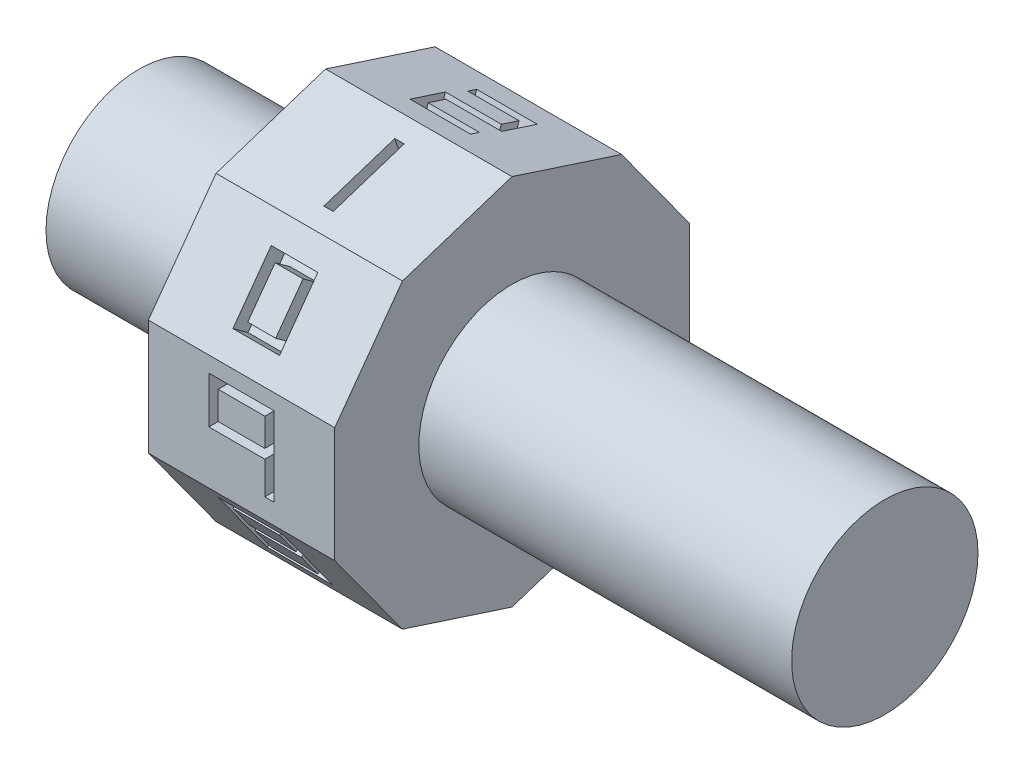
SolidWorks part; units mm, degrees
ref_plane "Front Plane" through (0, 0, 0) normal (0, 0, 1) x (1, 0, 0)
ref_plane "Top Plane" through (0, 0, 0) normal (0, 1, 0) x (1, 0, 0)
ref_plane "Right Plane" through (0, 0, 0) normal (1, 0, 0) x (0, 0, -1)
sketch "Sketch1" plane through (0, 0, 0) normal (1, 0, 0) x (0, 0, -1)
  line L1 (0, 25.4) -> (-14.9297, 20.549)
  line L2 (-14.9297, 20.549) -> (-24.1568, 7.849)
  line L3 (-24.1568, 7.849) -> (-24.1568, -7.849)
  line L4 (-24.1568, -7.849) -> (-14.9297, -20.549)
  line L5 (-14.9297, -20.549) -> (0, -25.4)
  line L6 (0, -25.4) -> (14.9297, -20.549)
  line L7 (14.9297, -20.549) -> (24.1568, -7.849)
  line L8 (24.1568, -7.849) -> (24.1568, 7.849)
  line L9 (24.1568, 7.849) -> (14.9297, 20.549)
  line L10 (14.9297, 20.549) -> (0, 25.4)
  circle A0 centre (0, 0) radius 24.1568 construction
  dimension "D1" = 25.4
extrude "Boss-Extrude1" add sketch "Sketch1" along normal blind 25.4
sketch "Sketch2" plane through (25.4, 0, 0) normal (1, 0, 0) x (0, 0, -1)
  circle A0 centre (0, 0) radius 12.7
  dimension "D1" = 25.4
extrude "Boss-Extrude2" add sketch "Sketch2" along normal blind 50.8
sketch "Sketch3" plane through (0, 0, 0) normal (-1, 0, 0) x (0, 0, 1)
  circle A0 centre (0, 0) radius 12.7
  dimension "D1" = 25.4
extrude "Boss-Extrude3" add sketch "Sketch3" along normal blind 25.4
sketch "Sketch4" plane through (0, 14.199, 19.5433) normal (0, 0.5878, 0.809) x (1, 0, 0)
  line L0 (0, 0) -> (25.4, 0) construction
  line L1 (25.4, -12.7) -> (25.4, 12.7) construction
  line L2 (12.7, 7.849) -> (12.7, -7.849) construction
  line L3 (25.4, 7.849) -> (0, 7.849) construction
  line L4 (25.4, -7.849) -> (0, -7.849) construction
  line L5 (10.16, 0) -> (15.24, 0)
  line L6 (15.24, -3.81) -> (15.24, 3.81)
  line L7 (10.16, -3.81) -> (10.16, 3.81)
  line L8 (10.16, 3.81) -> (15.24, 3.81)
  line L9 (10.16, -3.81) -> (15.24, -3.81)
  line L10 (10.795, 3.175) -> (14.605, 3.175)
  line L11 (14.605, -3.175) -> (14.605, 3.175)
  line L12 (10.795, -3.175) -> (14.605, -3.175)
  line L13 (10.795, -3.175) -> (10.795, 3.175)
  line L14 (9.525, 4.445) -> (15.875, 4.445)
  line L15 (15.875, -4.445) -> (15.875, 4.445)
  line L16 (9.525, -4.445) -> (15.875, -4.445)
  line L17 (9.525, -4.445) -> (9.525, 4.445)
  point P14 (12.7, 0)
  point P17 (15.24, 0)
  point P20 (10.16, 0)
  dimension "D1" = 5.08
  dimension "D2" = 7.62
  dimension "D3" = 0.635
  dimension "D4" = 0.635
extrude "Cut-Extrude1" cut sketch "Sketch4" against normal blind 2.54 contours L14 L15 L16 L17 | L10 L11 L12 L13
sketch "Sketch5" plane through (0, 22.9745, 7.4649) normal (0, 0.9511, 0.309) x (1, 0, 0)
  line L0 (12.7, -7.849) -> (12.7, 7.849) construction
  line L1 (25.4, -7.849) -> (0, -7.849) construction
  line L2 (25.4, 7.849) -> (0, 7.849) construction
  line L3 (12.7, -5.08) -> (12.7, 5.08)
  line L4 (13.335, -5.08) -> (13.335, 5.08)
  line L5 (12.065, -5.08) -> (12.065, 5.08)
  line L6 (12.065, 5.08) -> (13.335, 5.08)
  line L7 (13.335, -5.08) -> (12.065, -5.08)
  point P9 (12.7, 0)
  dimension "D1" = 10.16
  dimension "D2" = 0.635
  dimension "D3" = 0.635
extrude "Cut-Extrude2" cut sketch "Sketch5" against normal blind 2.54 contours L5 L6 L4 L7
sketch "Sketch6" plane through (0, 22.9745, -7.4649) normal (0, 0.9511, -0.309) x (1, 0, 0)
  line L0 (12.7, 7.849) -> (12.7, -7.849) construction
  line L1 (25.4, 7.849) -> (0, 7.849) construction
  line L2 (25.4, -7.849) -> (0, -7.849) construction
  line L3 (8.89, 3.81) -> (16.51, 3.81)
  line L4 (8.89, 0) -> (16.51, 0)
  line L5 (8.89, -3.81) -> (16.51, -3.81)
  line L6 (16.51, 3.81) -> (16.51, 0)
  line L7 (8.89, 0) -> (8.89, -3.81)
  line L8 (8.89, 3.175) -> (15.875, 3.175)
  line L9 (15.875, 3.175) -> (15.875, 0.635)
  line L10 (8.255, 0.635) -> (15.875, 0.635)
  line L11 (8.255, 0.635) -> (8.255, -4.445)
  line L12 (8.255, -4.445) -> (16.51, -4.445)
  line L13 (8.89, 4.445) -> (17.145, 4.445)
  line L14 (17.145, 4.445) -> (17.145, -0.635)
  line L15 (9.525, -0.635) -> (17.145, -0.635)
  line L16 (9.525, -0.635) -> (9.525, -3.175)
  line L17 (9.525, -3.175) -> (16.51, -3.175)
  line L18 (8.89, 4.445) -> (8.89, 3.175)
  line L19 (16.51, -3.175) -> (16.51, -4.445)
  point P9 (12.7, 3.81)
  point P13 (12.7, 0)
  point P16 (12.7, -3.81)
  dimension "D1" = 3.81
  dimension "D2" = 3.81
  dimension "D3" = 7.62
  dimension "D4" = 0.635
  dimension "D5" = 0.635
extrude "Cut-Extrude3" cut sketch "Sketch6" against normal blind 2.54 contours L8 L9 L10 L11 L12 L19 L17 L16 L15 L14 L13 L18
sketch "Sketch8" plane through (0, 14.199, -19.5433) normal (0, 0.5878, -0.809) x (-1, 0, 0)
  line L0 (-12.7, 7.849) -> (-12.7, -7.849) construction
  line L1 (-25.4, 7.849) -> (0, 7.849) construction
  line L2 (-25.4, -7.849) -> (0, -7.849) construction
  line L3 (-8.89, -5.08) -> (-16.51, -5.08)
  line L4 (-8.89, 0) -> (-16.51, 0)
  line L5 (-8.89, 5.08) -> (-16.51, 5.08)
  line L6 (-16.51, -5.08) -> (-16.51, 5.08)
  line L7 (-8.89, -4.445) -> (-15.875, -4.445)
  line L8 (-15.875, -4.445) -> (-15.875, 4.445)
  line L9 (-8.89, 4.445) -> (-15.875, 4.445)
  line L10 (-8.89, 0.635) -> (-16.51, 0.635)
  line L11 (-8.89, -5.715) -> (-17.145, -5.715)
  line L12 (-17.145, -5.715) -> (-17.145, 5.715)
  line L13 (-8.89, 5.715) -> (-17.145, 5.715)
  line L14 (-8.89, -0.635) -> (-16.51, -0.635)
  line L15 (-8.89, -5.715) -> (-8.89, -4.445)
  line L16 (-8.89, -0.635) -> (-8.89, 0.635)
  line L17 (-8.89, 4.445) -> (-8.89, 5.715)
  point P9 (-12.7, -5.08)
  point P13 (-12.7, 0)
  point P16 (-12.7, 5.08)
  dimension "D1" = 10.16
  dimension "D2" = 5.08
  dimension "D3" = 7.62
  dimension "D4" = 0.635
  dimension "D5" = 0.635
extrude "Cut-Extrude4" cut sketch "Sketch8" against normal blind 2.54 contours L7 L0 L3 L15 | L3 L0 L11 L15 | L0 L13 L12 L11 L3 L6 L5 | L0 L7 L8 L14 L6 L3 | L0 L4 L8 L14 | L14 L8 L4 L6 | L8 L10 L6 L4 | L0 L10 L8 L4 | L4 L0 L14 L16 | L10 L0 L4 L16 | L0 L5 L6 L10 L8 L9 | L5 L0 L9 L17 | L13 L0 L5 L17
sketch "Sketch9" plane through (0, 0, -24.1568) normal (0, 0, -1) x (-1, 0, 0)
  line L0 (-12.7, -7.849) -> (-12.7, 7.849) construction
  line L1 (-25.4, -7.849) -> (0, -7.849) construction
  line L2 (-25.4, 7.849) -> (0, 7.849) construction
  line L3 (-8.89, 0) -> (-16.51, 0)
  line L4 (-16.51, 5.08) -> (-16.51, -5.08)
  line L5 (-8.89, 0) -> (-8.89, -5.08)
  line L6 (-9.525, -0.635) -> (-16.51, -0.635)
  line L7 (-9.525, -0.635) -> (-9.525, -5.08)
  line L8 (-17.145, 5.08) -> (-17.145, -5.08)
  line L9 (-8.255, 0.635) -> (-16.51, 0.635)
  line L10 (-8.255, 0.635) -> (-8.255, -5.08)
  line L11 (-15.875, 5.08) -> (-15.875, -5.08)
  line L12 (-8.255, -5.08) -> (-9.525, -5.08)
  line L13 (-15.875, -5.08) -> (-17.145, -5.08)
  line L14 (-17.145, 5.08) -> (-15.875, 5.08)
  point P10 (-12.7, 0)
  point P12 (-16.51, 0)
  dimension "D1" = 10.16
  dimension "D2" = 7.62
  dimension "D3" = 5.08
  dimension "D4" = 0.635
  dimension "D5" = 0.635
extrude "Cut-Extrude5" cut sketch "Sketch9" against normal blind 2.54 contours L0 L6 L7 L12 L5 L3 | L0 L3 L5 L12 L10 L9 | L6 L0 L3 L11 | L3 L0 L9 L11 | L11 L3 L4 L6 | L11 L9 L4 L3 | L13 L11 L6 L4 | L14 L8 L13 L4 | L14 L4 L9 L11
sketch "Sketch10" plane through (0, -14.199, -19.5433) normal (0, -0.5878, -0.809) x (-1, 0, 0)
  line L0 (-12.7, -7.849) -> (-12.7, 7.849) construction
  line L1 (-25.4, -7.849) -> (0, -7.849) construction
  line L2 (-25.4, 7.849) -> (0, 7.849) construction
  line L3 (-8.89, 0) -> (-16.51, 0)
  line L4 (-8.89, -5.08) -> (-16.51, -5.08)
  line L5 (-8.89, 5.08) -> (-16.51, 5.08)
  line L6 (-8.89, -5.08) -> (-8.89, 0)
  line L7 (-16.51, 0) -> (-16.51, 5.08)
  line L8 (-8.89, 5.715) -> (-17.145, 5.715)
  line L9 (-17.145, -0.635) -> (-17.145, 5.715)
  line L10 (-9.525, -0.635) -> (-17.145, -0.635)
  line L11 (-9.525, -4.445) -> (-9.525, -0.635)
  line L12 (-9.525, -4.445) -> (-16.51, -4.445)
  line L13 (-8.89, 4.445) -> (-15.875, 4.445)
  line L14 (-15.875, 0.635) -> (-15.875, 4.445)
  line L15 (-8.255, 0.635) -> (-15.875, 0.635)
  line L16 (-8.255, -5.715) -> (-8.255, 0.635)
  line L17 (-8.255, -5.715) -> (-16.51, -5.715)
  line L18 (-16.51, -5.715) -> (-16.51, -4.445)
  line L19 (-8.89, 4.445) -> (-8.89, 5.715)
  point P10 (-12.7, 0)
  point P13 (-12.7, -5.08)
  point P16 (-12.7, 5.08)
  dimension "D1" = 10.16
  dimension "D2" = 5.08
  dimension "D3" = 7.62
  dimension "D4" = 0.635
  dimension "D5" = 0.635
extrude "Cut-Extrude6" cut sketch "Sketch10" against normal blind 2.54 contours L12 L18 L17 L16 L15 L14 L13 L19 L8 L9 L10 L11
sketch "Sketch11" plane through (0, -22.9745, -7.4649) normal (0, -0.9511, -0.309) x (1, 0, 0)
  line L0 (12.7, 7.849) -> (12.7, -7.849) construction
  line L1 (25.4, 7.849) -> (0, 7.849) construction
  line L2 (25.4, -7.849) -> (0, -7.849) construction
  line L3 (8.89, 5.08) -> (16.51, 5.08)
  line L4 (16.51, 0) -> (9.525, 0)
  line L5 (8.89, -5.08) -> (16.51, -5.08)
  line L6 (16.51, 0) -> (16.51, -5.08)
  line L7 (8.89, -5.08) -> (8.89, 5.08)
  line L8 (15.875, -0.635) -> (9.525, -0.635)
  line L9 (15.875, -0.635) -> (15.875, -4.445)
  line L10 (9.525, -4.445) -> (15.875, -4.445)
  line L11 (9.525, -4.445) -> (9.525, 4.445)
  line L12 (9.525, 4.445) -> (16.51, 4.445)
  line L13 (17.145, 0.635) -> (9.525, 0.635)
  line L14 (17.145, 0.635) -> (17.145, -5.715)
  line L15 (8.255, -5.715) -> (17.145, -5.715)
  line L16 (8.255, -5.715) -> (8.255, 5.715)
  line L17 (8.255, 5.715) -> (16.51, 5.715)
  line L18 (16.51, 5.715) -> (16.51, 4.445)
  point P9 (12.7, 5.08)
  point P13 (12.7, 0)
  point P16 (12.7, -5.08)
  dimension "D1" = 5.08
  dimension "D2" = 10.16
  dimension "D3" = 7.62
  dimension "D4" = 6.985
  dimension "D5" = 0.635
  dimension "D6" = 0.635
extrude "Cut-Extrude7" cut sketch "Sketch11" against normal blind 2.54 and the other way through all contours L0 L3 L7 L5 L10 L11 L12 | L0 L17 L16 L15 L5 L7 L3 | L17 L0 L3 L18 | L3 L0 L12 L18 | L0 L13 L11 L4 | L0 L4 L11 L8 | L13 L0 L4 L6 L5 L15 L14 | L4 L0 L8 L9 L10 L5 L6
sketch "Sketch12" plane through (0, -22.9745, 7.4649) normal (0, -0.9511, 0.309) x (1, 0, 0)
  line L0 (12.7, 7.849) -> (12.7, -7.849) construction
  line L1 (25.4, 7.849) -> (0, 7.849) construction
  line L2 (25.4, -7.849) -> (0, -7.849) construction
  line L3 (8.89, 5.08) -> (16.51, 5.08)
  line L4 (16.51, 5.08) -> (16.51, -5.08)
  line L5 (8.89, 4.445) -> (15.875, 4.445)
  line L6 (15.875, 4.445) -> (15.875, -5.08)
  line L7 (8.89, 5.715) -> (17.145, 5.715)
  line L8 (17.145, 5.715) -> (17.145, -5.08)
  line L9 (8.89, 5.715) -> (8.89, 4.445)
  line L10 (15.875, -5.08) -> (17.145, -5.08)
  point P6 (16.51, 0)
  point P9 (12.7, 5.08)
  point P11 (12.7, 0)
  dimension "D1" = 7.62
  dimension "D2" = 10.16
  dimension "D3" = 0.635
  dimension "D4" = 0.635
extrude "Cut-Extrude8" cut sketch "Sketch12" against normal blind 2.54 contours L7 L8 L10 L6 L5 L9
sketch "Sketch13" plane through (0, -14.199, 19.5433) normal (0, -0.5878, 0.809) x (1, 0, 0)
  line L0 (12.7, 7.849) -> (12.7, -7.849) construction
  line L1 (25.4, 7.849) -> (0, 7.849) construction
  line L2 (25.4, -7.849) -> (0, -7.849) construction
  line L3 (9.525, 0) -> (15.875, 0)
  line L4 (8.89, 5.08) -> (16.51, 5.08)
  line L5 (8.89, -5.08) -> (16.51, -5.08)
  line L6 (16.51, 5.08) -> (16.51, -5.08)
  line L7 (8.89, 5.08) -> (8.89, -5.08)
  line L8 (8.255, 5.715) -> (17.145, 5.715)
  line L9 (17.145, 5.715) -> (17.145, -5.715)
  line L10 (8.255, -5.715) -> (17.145, -5.715)
  line L11 (8.255, 5.715) -> (8.255, -5.715)
  line L12 (9.525, -0.635) -> (15.875, -0.635)
  line L13 (9.525, 4.445) -> (15.875, 4.445)
  line L14 (15.875, 4.445) -> (15.875, -4.445)
  line L15 (9.525, -4.445) -> (15.875, -4.445)
  line L16 (9.525, 4.445) -> (9.525, -4.445)
  line L17 (9.525, 0.635) -> (15.875, 0.635)
  point P10 (12.7, 0)
  point P13 (12.7, 5.08)
  point P16 (12.7, -5.08)
  point P17 (12.7, 0)
  dimension "D1" = 10.16
  dimension "D2" = 6.35
  dimension "D3" = 7.62
  dimension "D4" = 5.08
  dimension "D5" = 0.635
  dimension "D6" = 0.635
extrude "Cut-Extrude9" cut sketch "Sketch13" against normal blind 2.54 contours L0 L8 L11 L10 L5 L7 L4 | L0 L4 L7 L5 L15 L16 L13 | L4 L0 L13 L14 L15 L5 L6 | L8 L0 L4 L6 L5 L10 L9 | L17 L0 L3 L14 | L0 L17 L16 L3 | L0 L3 L16 L12 | L3 L0 L12 L14
sketch "Sketch14" plane through (0, 0, 24.1568) normal (0, 0, 1) x (1, 0, 0)
  line L0 (12.7, 7.849) -> (12.7, -7.849) construction
  line L1 (25.4, 7.849) -> (0, 7.849) construction
  line L2 (25.4, -7.849) -> (0, -7.849) construction
  line L3 (9.525, 0) -> (15.875, 0)
  line L4 (8.89, 5.08) -> (16.51, 5.08)
  line L5 (16.51, 5.08) -> (16.51, -5.08)
  line L6 (8.89, 5.08) -> (8.89, 0)
  line L7 (17.145, 5.715) -> (17.145, -5.08)
  line L8 (8.255, 5.715) -> (17.145, 5.715)
  line L9 (8.255, 5.715) -> (8.255, 0)
  line L10 (9.525, -0.635) -> (15.875, -0.635)
  line L11 (15.875, 4.445) -> (15.875, -5.08)
  line L12 (9.525, 4.445) -> (15.875, 4.445)
  line L13 (9.525, 4.445) -> (9.525, 0)
  line L14 (9.525, 0.635) -> (15.875, 0.635)
  line L15 (8.255, 0) -> (8.255, -0.635)
  line L16 (15.875, -5.08) -> (17.145, -5.08)
  line L17 (8.255, -0.635) -> (9.525, -0.635)
  line L18 (8.89, 0) -> (9.525, 0)
  point P10 (12.7, 0)
  point P13 (12.7, 5.08)
  dimension "D1" = 7.62
  dimension "D2" = 10.16
  dimension "D3" = 5.08
  dimension "D4" = 5.08
  dimension "D5" = 6.35
  dimension "D6" = 0.635
  dimension "D7" = 0.635
extrude "Cut-Extrude10" cut sketch "Sketch14" against normal blind 2.54 and the other way through all contours L0 L4 L6 L18 L13 L12 | L0 L8 L9 L15 L17 L10 L3 L18 L6 L4 | L0 L14 L13 L3 | L14 L0 L3 L11 | L3 L0 L10 L11 | L4 L0 L12 L11 L16 L5 | L8 L0 L4 L5 L16 L7
